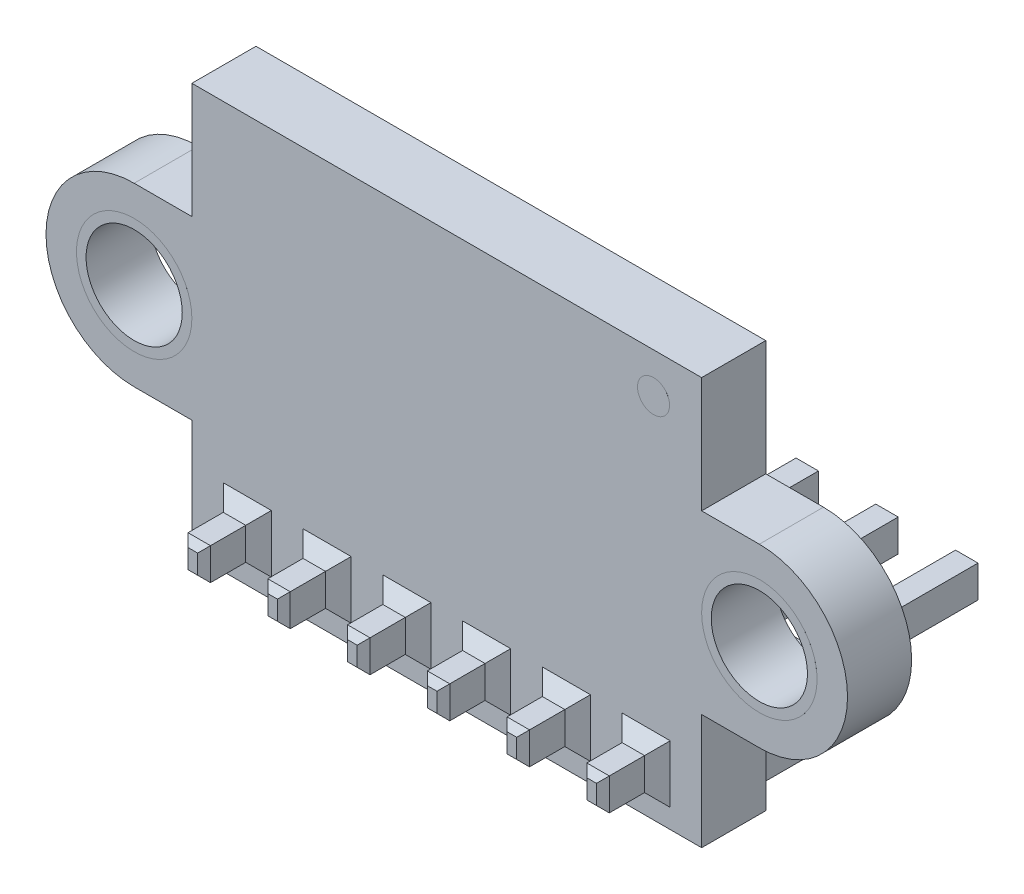
SolidWorks part; units mm, degrees
ref_plane "Plano frontal" through (0, 0, 0) normal (0, 0, 1) x (1, 0, 0)
ref_plane "Plano superior" through (0, 0, 0) normal (0, 1, 0) x (1, 0, 0)
ref_plane "Plano direito" through (0, 0, 0) normal (1, 0, 0) x (0, 0, -1)
sketch "Sketch1" plane through (0, 0, 0) normal (0, 0, 1) x (1, 0, 0)
  line L1 (7.95, -6.35) -> (-7.95, -6.35)
  line L2 (7.95, -6.35) -> (7.95, 6.35)
  line L3 (7.95, 6.35) -> (-7.95, 6.35)
  line L4 (-7.95, -6.35) -> (-7.95, 6.35)
  line L5 (7.95, -6.35) -> (-7.95, 6.35) construction
  line L6 (7.95, 6.35) -> (-7.95, -6.35) construction
  point P0 (0, 0)
  dimension "D1" = 15.9
  dimension "D2" = 12.7
extrude "Boss-Extrude1" add sketch "Sketch1" along normal mid plane 2
sketch "Sketch2" plane through (0, 0, 0) normal (0, 0, 1) x (1, 0, 0)
  line L0 (0, -6.545) -> (0, 6.545) construction
  line L1 (-9.75, 2.75) -> (-9.75, -2.75) construction
  line L2 (-9.75, 2.75) -> (-7.95, 2.75)
  line L3 (-7.95, 6.35) -> (-7.95, -6.35) construction
  line L4 (-9.75, -2.75) -> (-7.95, -2.75)
  line L5 (9.75, -2.75) -> (7.95, -2.75)
  line L6 (9.75, 2.75) -> (7.95, 2.75)
  line L7 (-7.95, 2.75) -> (-7.95, -2.75)
  line L8 (7.95, 2.75) -> (7.95, -2.75)
  circle A0 centre (-9.75, 0) radius 1.5
  circle A1 centre (9.75, 0) radius 1.5
  arc A2 (-9.75, 2.75) -> (-9.75, -2.75) centre (-9.75, 0) ccw
  arc A3 (9.75, 2.75) -> (9.75, -2.75) centre (9.75, 0) cw
  dimension "D1" = 3
  dimension "D2" = 25
  dimension "D3" = 1.25
  dimension "D4" = 19.5
extrude "Boss-Extrude2" add sketch "Sketch2" along normal mid plane 2
sketch "Sketch3" plane through (0, 0, -1) normal (0, 0, -1) x (-1, 0, 0)
  line L0 (-7.95, -6.35) -> (-7.95, -2.75) construction
  line L1 (-7.8, -3.5) -> (7.8, -3.5)
  line L2 (-7.8, -3.5) -> (-7.8, -6.2)
  line L3 (-7.8, -6.2) -> (7.8, -6.2)
  line L4 (7.8, -3.5) -> (7.8, -6.2)
  line L5 (7.95, -6.35) -> (-7.95, -6.35) construction
  point P8 (0, -3.5)
  dimension "D1" = 0.15
  dimension "D2" = 2.7
  dimension "D3" = 0.15
  dimension "D4" = 15.6
extrude "Boss-Extrude3" add sketch "Sketch3" along normal blind 2.3
chamfer "Chamfer1" distance 0.5 angle 45 4 edges at (-7.8, -3.5, -2.15) (7.8, -3.5, -2.15) (7.8, -6.2, -2.15) (-7.8, -6.2, -2.15)
sketch "Sketch4" plane through (0, 0, -3.3) normal (0, 0, -1) x (-1, 0, 0)
  line L0 (-7.8, -4) -> (-7.8, -5.7) construction
  line L1 (-6.57, -4.35) -> (6.57, -4.35) construction
  line L2 (-6.57, -4.35) -> (-6.57, -5.35) construction
  line L3 (-6.57, -5.35) -> (6.57, -5.35) construction
  line L4 (6.57, -4.35) -> (6.57, -5.35) construction
  line L5 (-4.082, -4.35) -> (-3.382, -4.35)
  line L6 (-6.57, -4.35) -> (-5.87, -4.35)
  line L7 (-6.57, -4.35) -> (-6.57, -5.35)
  line L8 (-6.57, -5.35) -> (-5.87, -5.35)
  line L9 (-5.87, -4.35) -> (-5.87, -5.35)
  line L10 (-4.082, -4.35) -> (-4.082, -5.35)
  line L11 (-4.082, -5.35) -> (-3.382, -5.35)
  line L12 (-3.382, -4.35) -> (-3.382, -5.35)
  line L13 (-4.082, -4.35) -> (-4.082, -5.35) construction
  line L14 (-1.594, -4.35) -> (-0.894, -4.35)
  line L15 (-1.594, -4.35) -> (-1.594, -5.35)
  line L16 (-1.594, -5.35) -> (-0.894, -5.35)
  line L17 (-0.894, -4.35) -> (-0.894, -5.35)
  line L18 (-1.594, -4.35) -> (-1.594, -5.35) construction
  line L19 (0.894, -4.35) -> (1.594, -4.35)
  line L20 (0.894, -4.35) -> (0.894, -5.35)
  line L21 (0.894, -5.35) -> (1.594, -5.35)
  line L22 (1.594, -4.35) -> (1.594, -5.35)
  line L23 (0.894, -4.35) -> (0.894, -5.35) construction
  line L24 (3.382, -4.35) -> (4.082, -4.35)
  line L25 (3.382, -4.35) -> (3.382, -5.35)
  line L26 (3.382, -5.35) -> (4.082, -5.35)
  line L27 (4.082, -4.35) -> (4.082, -5.35)
  line L28 (3.382, -4.35) -> (3.382, -5.35) construction
  line L29 (5.87, -4.35) -> (6.57, -4.35)
  line L30 (5.87, -4.35) -> (5.87, -5.35)
  line L31 (5.87, -5.35) -> (6.57, -5.35)
  line L32 (6.57, -4.35) -> (6.57, -5.35)
  line L33 (5.87, -4.35) -> (5.87, -5.35) construction
  point P4 (0, -4.35)
  point P8 (-7.8, -4.85)
  point P9 (-6.57, -4.85)
  dimension "D1" = 13.14
  dimension "D2" = 1
  dimension "D3" = 0.7
  dimension "D4" = 6
extrude "Boss-Extrude4" add sketch "Sketch4" along normal blind 5.9 and the other way blind 6
chamfer "Chamfer2" distance 0.2 angle 45 48 edges at (-6.22, -4.35, -9.2) (-6.57, -4.85, -9.2) (-6.22, -5.35, -9.2) (-5.87, -4.85, -9.2) (-3.732, -4.35, -9.2) (-4.082, -4.85, -9.2) (-3.732, -5.35, -9.2) (-3.382, -4.85, -9.2) (-1.244, -4.35, -9.2) (-1.594, -4.85, -9.2) (-1.244, -5.35, -9.2) (-0.894, -4.85, -9.2) (1.244, -4.35, -9.2) (0.894, -4.85, -9.2) (1.244, -5.35, -9.2) (1.594, -4.85, -9.2) (3.732, -4.35, -9.2) (3.382, -4.85, -9.2) (3.732, -5.35, -9.2) (4.082, -4.85, -9.2) (6.22, -4.35, -9.2) (5.87, -4.85, -9.2) (6.22, -5.35, -9.2) (6.57, -4.85, -9.2) (-6.22, -5.35, 2.7) (-6.57, -4.85, 2.7) (-6.22, -4.35, 2.7) (-5.87, -4.85, 2.7) (-3.732, -5.35, 2.7) (-4.082, -4.85, 2.7) (-3.732, -4.35, 2.7) (-3.382, -4.85, 2.7) (-1.244, -5.35, 2.7) (-1.594, -4.85, 2.7) (-1.244, -4.35, 2.7) (-0.894, -4.85, 2.7) (1.244, -5.35, 2.7) (0.894, -4.85, 2.7) (1.244, -4.35, 2.7) (1.594, -4.85, 2.7) (3.732, -5.35, 2.7) (3.382, -4.85, 2.7) (3.732, -4.35, 2.7) (4.082, -4.85, 2.7) (6.22, -5.35, 2.7) (5.87, -4.85, 2.7) (6.22, -4.35, 2.7) (6.57, -4.85, 2.7)
chamfer "Chamfer3" distance 0.4 angle 45 24 edges at (-6.22, -4.35, 1) (-6.57, -4.85, 1) (-6.22, -5.35, 1) (-5.87, -4.85, 1) (-3.732, -4.35, 1) (-4.082, -4.85, 1) (-3.732, -5.35, 1) (-3.382, -4.85, 1) (-1.244, -4.35, 1) (-1.594, -4.85, 1) (-1.244, -5.35, 1) (-0.894, -4.85, 1) (1.244, -4.35, 1) (0.894, -4.85, 1) (1.244, -5.35, 1) (1.594, -4.85, 1) (3.732, -4.35, 1) (3.382, -4.85, 1) (3.732, -5.35, 1) (4.082, -4.85, 1) (6.22, -4.35, 1) (5.87, -4.85, 1) (6.22, -5.35, 1) (6.57, -4.85, 1)
sketch "Sketch5" plane through (0, 0, 1) normal (0, 0, 1) x (1, 0, 0)
  line L0 (0, -1.1) -> (0, 1.1) construction
  line L2 (7.95, 2.75) -> (7.95, 6.35) construction
  line L3 (7.95, 6.35) -> (-7.95, 6.35) construction
  circle A0 centre (-9.75, 0) radius 1.5 construction
  circle A1 centre (-9.75, 0) radius 1.5
  circle A2 centre (-9.75, 0) radius 1.8
  circle A3 centre (9.75, 0) radius 1.5
  circle A4 centre (9.75, 0) radius 1.8
  circle A5 centre (6.45, 5.1) radius 0.5
  dimension "D2" = 1
  dimension "D3" = 1
  dimension "D4" = 0.75
  dimension "D1" = 0.3
extrude "Boss-Extrude5" add sketch "Sketch5" along normal blind 0.0001
